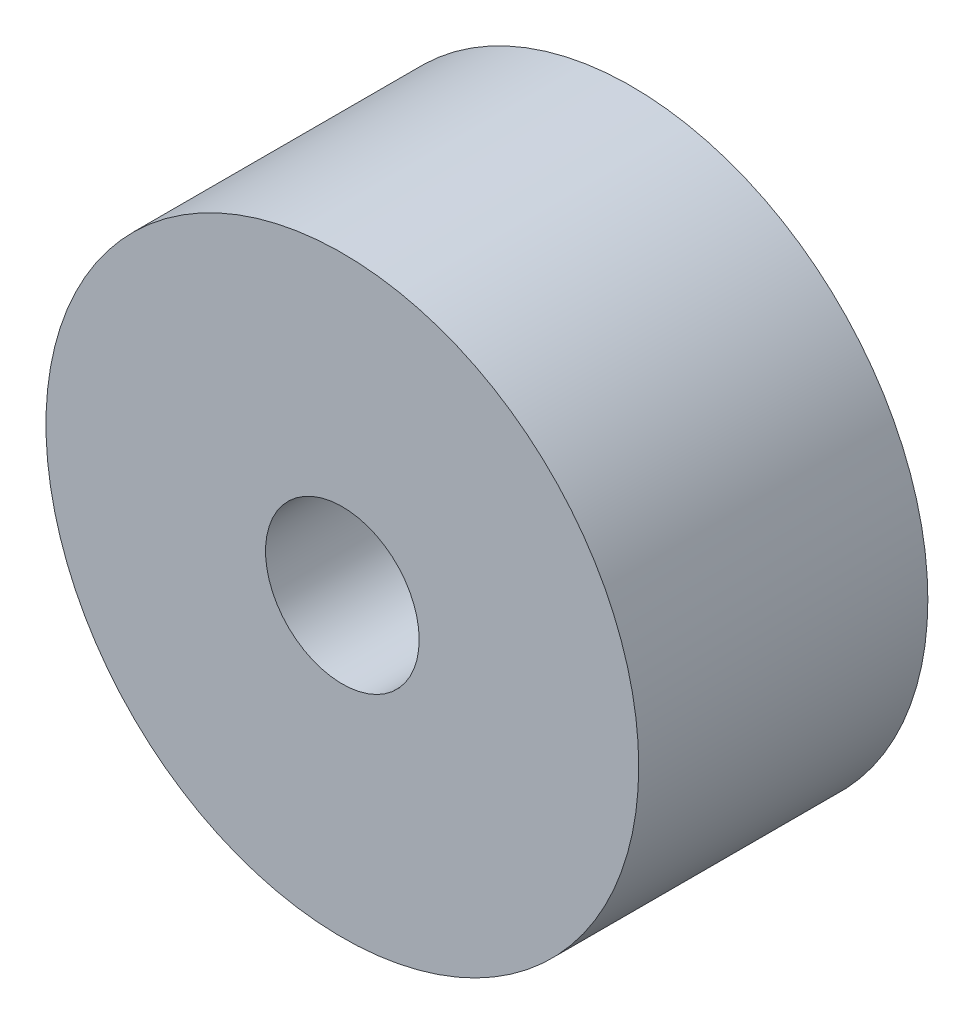
SolidWorks part; units mm, degrees
ref_plane "前视基准面" through (0, 0, 0) normal (0, 0, 1) x (1, 0, 0)
ref_plane "上视基准面" through (0, 0, 0) normal (0, 1, 0) x (1, 0, 0)
ref_plane "右视基准面" through (0, 0, 0) normal (1, 0, 0) x (0, 0, -1)
sketch "草图1" plane through (0, 0, 0) normal (0, 0, 1) x (1, 0, 0)
  circle A0 centre (0, 0) radius 24.5
  dimension "D1" = 49
extrude "凸台-拉伸1" add sketch "草图1" along normal blind 23.9
sketch "草图2" plane through (0, 0, 23.9) normal (0, 0, 1) x (1, 0, 0)
  circle A0 centre (0, 0) radius 6.35
  dimension "D1" = 12.7
extrude "切除-拉伸1" cut sketch "草图2" against normal blind 10
sketch "草图3" plane through (0, 0, 23.9) normal (0, 0, 1) x (1, 0, 0)
  line L0 (-33.3796, 0) -> (46.8719, 0) construction
  line L1 (0, 26.0061) -> (0, -31.3898) construction
  line L2 (0, 0) -> (-8.8388, 8.8388) construction
  line L3 (0, 0) -> (-8.8388, -8.8388) construction
  line L4 (0, 0) -> (8.8388, 8.8388) construction
  line L5 (9.3184, -8.3317) -> (0, 0) construction
  circle A0 centre (0, 0) radius 22 construction
  circle A1 centre (0, 0) radius 12.5 construction
  circle A2 centre (-8.8388, 8.8388) radius 1.5
  circle A3 centre (-8.8388, -8.8388) radius 1.5
  circle A4 centre (8.8388, 8.8388) radius 1.5
  circle A6 centre (9.3184, -8.3317) radius 1.5
  circle A7 centre (-15.5563, 15.5563) radius 1.25
  point P18 (0, 0)
  point P19 (0, 0)
  dimension "D1" = 44
  dimension "D2" = 25
  dimension "D3" = 3
  dimension "D4" = 3
  dimension "D5" = 3
  dimension "D6" = 3
  dimension "D11" = 2.5
  dimension "D7" = 45
  dimension "D8" = 45
  dimension "D9" = 45
  dimension "D10" = 48.2
